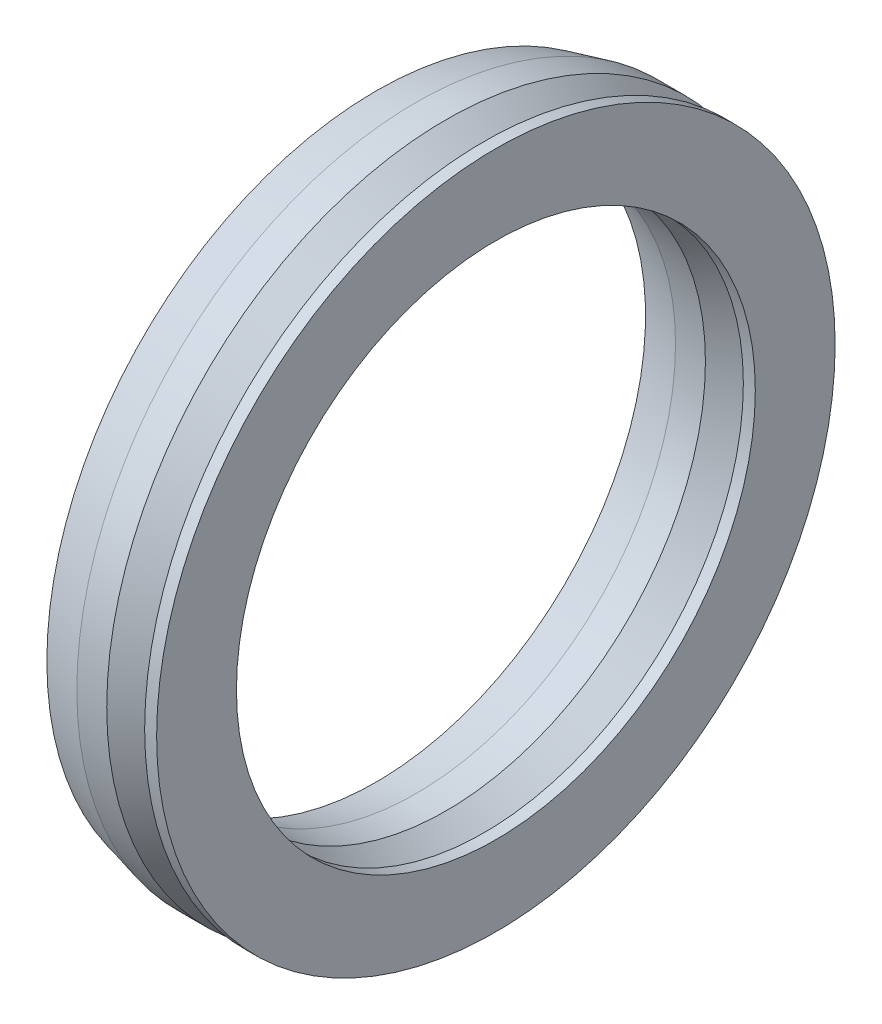
SolidWorks part; units mm, degrees
other "Hydrostatic"
material "PCTFE"
ref_plane "Front Plane" through (0, 0, 0) normal (0, 0, 1) x (1, 0, 0)
ref_plane "Top Plane" through (0, 0, 0) normal (0, 1, 0) x (1, 0, 0)
ref_plane "Right Plane" through (0, 0, 0) normal (1, 0, 0) x (0, 0, -1)
sketch "Sketch1" plane through (0, 0, 0) normal (0, 0, 1) x (1, 0, 0)
  line L0 (-63.8266, 0) -> (71.7732, 0) construction
  line L1 (-24.9993, 30) -> (6.449, 30) construction
  line L2 (0, 34) -> (0, 26)
  line L3 (0, 26) -> (-1.2, 26)
  line L4 (-1.2, 26) -> (-1.2, 28.5)
  line L5 (-1.2, 28.5) -> (-2.2, 28.5)
  line L6 (-2.2, 28.5) -> (-2.2, 28)
  line L7 (-5, 26) -> (-8, 26)
  line L8 (-8, 26) -> (-12, 27)
  line L9 (-12, 27) -> (-12, 28)
  line L10 (-12, 28) -> (-8, 27)
  line L15 (-8, 27) -> (-3, 30)
  line L16 (-8, 33) -> (-3, 30)
  line L17 (-12, 32) -> (-8, 33)
  line L18 (-12, 33) -> (-12, 32)
  line L19 (-8, 34) -> (-12, 33)
  line L23 (-2.2, 31.5) -> (-2.2, 32)
  line L24 (-1.2, 31.5) -> (-2.2, 31.5)
  line L25 (-1.2, 34) -> (-1.2, 31.5)
  line L26 (0, 34) -> (-1.2, 34)
  line L27 (-5, 26) -> (-2.2, 28)
  line L28 (-5, 34) -> (-2.2, 32)
  line L29 (-5, 34) -> (-8, 34)
  point P11 (-5.2124, 27)
  point P15 (-3.089, 30)
  point P17 (0, 0)
  point P24 (-8, 27)
  point P25 (-3, 29.6539)
  dimension "D1" = 4
  dimension "D2" = 1
  dimension "D3" = 3
  dimension "D4" = 1
  dimension "D5" = 2.5
  dimension "D6" = 1.2
  dimension "D7" = 12
  dimension "D8" = 1
  dimension "D10" = 30
  dimension "D9" = 5
  dimension "D11" = 2
  dimension "D12" = 3
revolve "Revolve2" add sketch "Sketch1" angle 360 about L0
equation "\"installed_length\"= 8mm"
equation "\"D1@Sketch1\"=\"installed_length\"/2"
equation "\"leadin_height\"= 1mm"
equation "\"D2@Sketch1\"=\"leadin_height\""
equation "\"seal_surface_length\"= 3mm"
equation "\"D3@Sketch1\"=\"seal_surface_length\""
equation "\"slot_width\"= 1mm"
equation "\"slot_height\"= 2.5mm"
equation "\"D5@Sketch1\"=\"slot_height\""
equation "\"D4@Sketch1\"=\"slot_width\""
equation "\"installed_height\" = 12mm"
equation "\"D7@Sketch1\"=\"installed_height\""
equation "\"radius\"= 30mm"
equation "\"D10@Sketch1\"=\"radius\""
